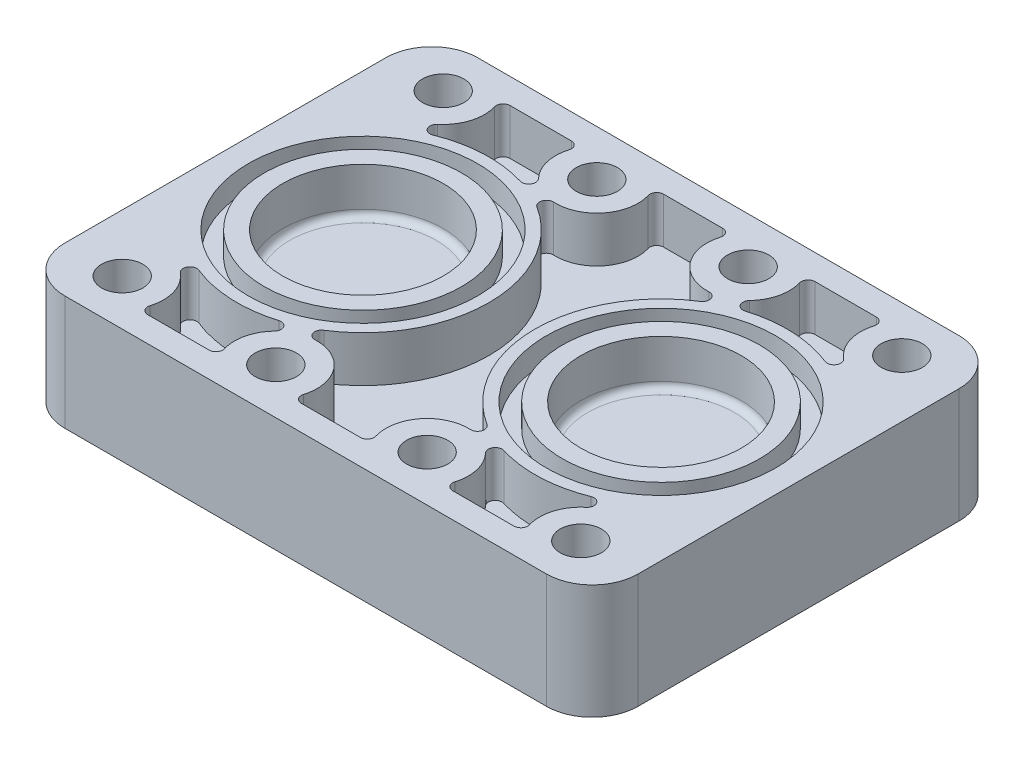
SolidWorks part; units mm, degrees
ref_plane "Front Plane" through (0, 0, 0) normal (0, 0, 1) x (1, 0, 0)
ref_plane "Top Plane" through (0, 0, 0) normal (0, 1, 0) x (1, 0, 0)
ref_plane "Right Plane" through (0, 0, 0) normal (1, 0, 0) x (0, 0, -1)
sketch "Sketch1" plane through (0, 0, 0) normal (0, 1, 0) x (1, 0, 0)
  line L0 (0, 0) -> (224.7644, 0) construction
  line L1 (224.7644, 0) -> (-243.6126, 0) construction
  line L2 (0, 0) -> (0, -121.8063) construction
  line L3 (0, -121.8063) -> (0, 105.7853) construction
  line L5 (-105, -90) -> (105, -90)
  line L6 (-125, -70) -> (-125, 70)
  line L7 (-105, 90) -> (105, 90)
  line L8 (125, -70) -> (125, 70)
  arc A0 (105, 90) -> (125, 70) centre (105, 70) cw
  arc A1 (125, -70) -> (105, -90) centre (105, -70) cw
  arc A2 (-125, -70) -> (-105, -90) centre (-105, -70) ccw
  arc A3 (-125, 70) -> (-105, 90) centre (-105, 70) cw
  point P10 (-125, 0)
  point P11 (0, 90)
  point P14 (125, 90)
  point P17 (125, -90)
  point P20 (-125, -90)
  dimension "D3" = 20
  dimension "D1" = 180
  dimension "D2" = 250
extrude "Boss-Extrude1" add sketch "Sketch1" along normal blind 50
sketch "Sketch2" plane through (0, 50, 0) normal (0, 1, 0) x (1, 0, 0)
  line L0 (0, 0) -> (200.7487, 0) construction
  line L1 (200.7487, 0) -> (-222.6486, 0) construction
  line L2 (0, 0) -> (0, 90) construction
  line L3 (105, 90) -> (-105, 90) construction
  line L4 (0, 90) -> (0, -108.891) construction
  line L5 (-105, -90) -> (105, -90) construction
  line L6 (125, -70) -> (125, 70) construction
  circle A0 centre (-100, -70) radius 9
  circle A1 centre (-33, -70) radius 9
  circle A2 centre (33, -70) radius 9
  circle A3 centre (100, -70) radius 9
  circle A4 centre (100, 70) radius 9
  circle A5 centre (33, 70) radius 9
  circle A6 centre (-33, 70) radius 9
  circle A7 centre (-100, 70) radius 9
  dimension "D1" = 18
  dimension "D2" = 20
  dimension "D3" = 20
  dimension "D4" = 20
  dimension "D5" = 20
  dimension "D6" = 67
  dimension "D7" = 67
  dimension "D8" = 66
  dimension "D9" = 25
extrude "Cut-Extrude1" cut sketch "Sketch2" against normal up to surface (50 mm away) up to face at (0, 0, 0)
ref_plane "Plane1" through (0, 35, 0) normal (0, 1, 0) x (1, 0, 0)
sketch "Sketch4" plane through (0, 35, 0) normal (0, 1, 0) x (1, 0, 0)
  line L0 (0, 0) -> (-194.5032, 0) construction
  circle A0 centre (-100, -70) radius 12.5
  circle A1 centre (-33, -70) radius 12.5
  circle A2 centre (33, -70) radius 12.5
  circle A3 centre (100, -70) radius 12.5
  circle A4 centre (100, 70) radius 12.5
  circle A5 centre (33, 70) radius 12.5
  circle A6 centre (-33, 70) radius 12.5
  circle A7 centre (-100, 70) radius 12.5
  dimension "D1" = 25
  dimension "D2" = 25
  dimension "D3" = 25
  dimension "D4" = 25
extrude "Cut-Extrude2" cut sketch "Sketch4" against normal up to surface (35 mm away) up to face at (-33, 0, 61)
sketch "Sketch7" plane through (0, 50, 0) normal (0, 1, 0) x (1, 0, 0)
  line L0 (0, 0) -> (194.9493, 0) construction
  line L1 (194.9493, 0) -> (-217.2547, 0) construction
  line L2 (0, 0) -> (0, 103.2741) construction
  line L3 (0, 103.2741) -> (0, -115.319) construction
  line L4 (-125, 70) -> (-125, -70) construction
  line L5 (125, -70) -> (125, 70) construction
  circle A2 centre (-65, 0) radius 35
  circle A3 centre (65, 0) radius 35
  point P2 (0, 0)
  dimension "D3" = 70
  dimension "D4" = 70
  dimension "D1" = 60
  dimension "D2" = 60
extrude "Cut-Extrude3" cut sketch "Sketch7" against normal blind 20
fillet "Fillet1" radius 3 2 edges at (65, 30, 35) (-65, 30, 35)
sketch "Sketch8" plane through (0, 50, 0) normal (0, 1, 0) x (1, 0, 0)
  line L0 (0, 0) -> (0, -113.0884) construction
  circle A0 centre (-65, 0) radius 43
  circle A1 centre (-65, 0) radius 50
  circle A2 centre (65, 0) radius 43
  circle A3 centre (65, 0) radius 50
  dimension "D1" = 86
  dimension "D2" = 100
extrude "Cut-Extrude4" cut sketch "Sketch8" against normal blind 10
sketch "Sketch9" plane through (0, 50, 0) normal (0, 1, 0) x (1, 0, 0)
  line L0 (0, 0) -> (0, -120.2262) construction
  line L2 (-53.1246, -79) -> (-79.8754, -79)
  line L3 (-204.9076, 0) -> (204.9076, 0) construction
  line L4 (53.1246, 79) -> (79.8754, 79)
  line L6 (-53.1246, 79) -> (-79.8754, 79)
  line L7 (-12.8754, -79) -> (12.8754, -79)
  line L8 (-12.8754, 79) -> (12.8754, 79)
  line L9 (53.1246, -79) -> (79.8754, -79)
  arc A7 (79.8754, 79) -> (82.7503, 75.1429) centre (79.8754, 76) cw
  arc A8 (50.2497, 75.1429) -> (53.1246, 79) centre (53.1246, 76) cw
  arc A9 (50.2497, 75.1429) -> (46.0327, 57.5843) centre (33, 70) cw
  arc A10 (49.0735, 52.6436) -> (46.0327, 57.5843) centre (48.2048, 55.5151) cw
  arc A11 (88.5203, 56.1357) -> (85.4895, 51.041) centre (86.6071, 53.825) cw
  arc A12 (88.5203, 56.1357) -> (82.7503, 75.1429) centre (100, 70) cw
  arc A13 (-79.8754, -79) -> (-82.7503, -75.1429) centre (-79.8754, -76) cw
  arc A14 (-50.2497, -75.1429) -> (-53.1246, -79) centre (-53.1246, -76) cw
  arc A15 (-88.5203, 56.1357) -> (-82.7503, 75.1429) centre (-100, 70) ccw
  arc A16 (-88.5203, 56.1357) -> (-85.4895, 51.041) centre (-86.6071, 53.825) ccw
  arc A17 (-49.0735, 52.6436) -> (-46.0327, 57.5843) centre (-48.2048, 55.5151) ccw
  arc A18 (-50.2497, 75.1429) -> (-46.0327, 57.5843) centre (-33, 70) ccw
  arc A19 (-50.2497, 75.1429) -> (-53.1246, 79) centre (-53.1246, 76) ccw
  arc A20 (-79.8754, 79) -> (-82.7503, 75.1429) centre (-79.8754, 76) ccw
  arc A21 (-50.2497, -75.1429) -> (-46.0327, -57.5843) centre (-33, -70) cw
  arc A22 (-49.0735, -52.6436) -> (-46.0327, -57.5843) centre (-48.2048, -55.5151) cw
  arc A23 (-88.5203, -56.1357) -> (-85.4895, -51.041) centre (-86.6071, -53.825) cw
  arc A25 (-85.4895, 51.041) -> (-49.0735, 52.6436) centre (-65, 0) cw
  arc A26 (-15.7503, -75.1429) -> (-33.8622, -52.0207) centre (-33, -70) ccw
  arc A27 (-35.609, -46.4884) -> (-33.8622, -52.0207) centre (-34.0058, -49.0241) ccw
  arc A28 (15.7503, -75.1429) -> (33.8622, -52.0207) centre (33, -70) cw
  arc A29 (35.609, -46.4884) -> (33.8622, -52.0207) centre (34.0058, -49.0241) cw
  arc A30 (-15.7503, -75.1429) -> (-12.8754, -79) centre (-12.8754, -76) ccw
  arc A31 (12.8754, -79) -> (15.7503, -75.1429) centre (12.8754, -76) ccw
  arc A33 (85.4895, -51.041) -> (49.0735, -52.6436) centre (65, 0) cw
  arc A34 (35.609, 46.4884) -> (33.8622, 52.0207) centre (34.0058, 49.0241) ccw
  arc A35 (15.7503, 75.1429) -> (33.8622, 52.0207) centre (33, 70) ccw
  arc A36 (12.8754, 79) -> (15.7503, 75.1429) centre (12.8754, 76) cw
  arc A37 (-15.7503, 75.1429) -> (-12.8754, 79) centre (-12.8754, 76) cw
  arc A38 (-15.7503, 75.1429) -> (-33.8622, 52.0207) centre (-33, 70) cw
  arc A39 (-35.609, 46.4884) -> (-33.8622, 52.0207) centre (-34.0058, 49.0241) cw
  arc A40 (-35.609, 46.4884) -> (-35.609, -46.4884) centre (-65, 0) cw
  arc A41 (-88.5203, -56.1357) -> (-82.7503, -75.1429) centre (-100, -70) cw
  arc A42 (85.4895, 51.041) -> (49.0735, 52.6436) centre (65, 0) ccw
  arc A43 (35.609, 46.4884) -> (35.609, -46.4884) centre (65, 0) ccw
  arc A44 (88.5203, -56.1357) -> (82.7503, -75.1429) centre (100, -70) ccw
  arc A45 (88.5203, -56.1357) -> (85.4895, -51.041) centre (86.6071, -53.825) ccw
  arc A46 (49.0735, -52.6436) -> (46.0327, -57.5843) centre (48.2048, -55.5151) ccw
  arc A47 (50.2497, -75.1429) -> (46.0327, -57.5843) centre (33, -70) ccw
  arc A48 (50.2497, -75.1429) -> (53.1246, -79) centre (53.1246, -76) ccw
  arc A49 (79.8754, -79) -> (82.7503, -75.1429) centre (79.8754, -76) ccw
  arc A50 (-85.4895, -51.041) -> (-49.0735, -52.6436) centre (-65, 0) ccw
  dimension "D9" = 6
  dimension "D10" = 6
  dimension "D11" = 6
extrude "Cut-Extrude5" cut sketch "Sketch9" against normal blind 20
